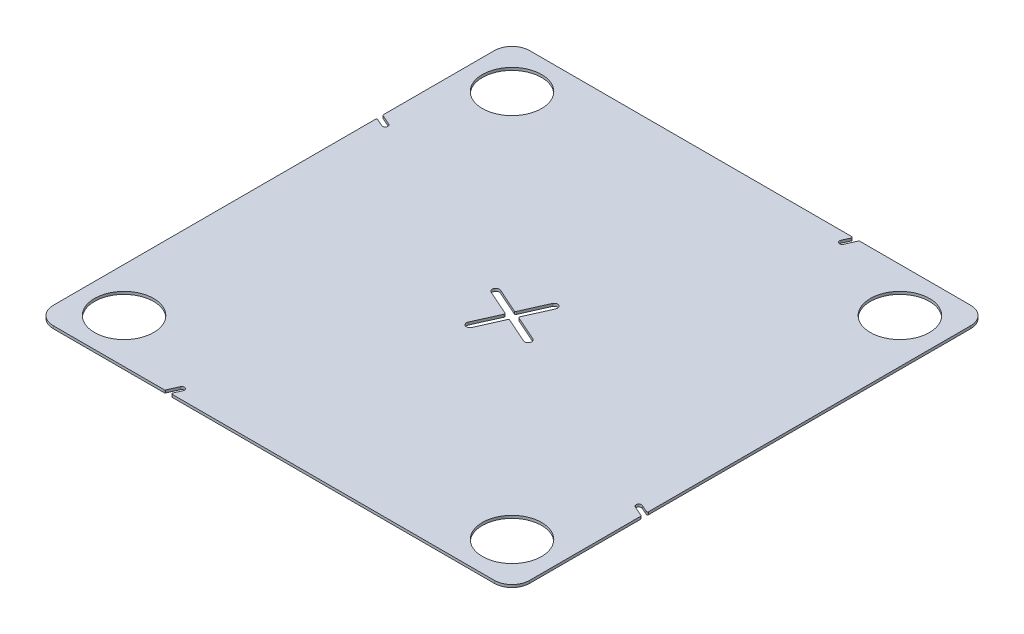
SolidWorks part; units mm, degrees
material "Plain Carbon Steel"
ref_plane "Front Plane" through (0, 0, 0) normal (0, 0, 1) x (1, 0, 0)
ref_plane "Top Plane" through (0, 0, 0) normal (0, 1, 0) x (1, 0, 0)
ref_plane "Right Plane" through (0, 0, 0) normal (1, 0, 0) x (0, 0, -1)
sketch "Sketch1" plane through (0, 0, 0) normal (0, 1, 0) x (1, 0, 0)
  line L0 (-228.092, -228.092) -> (-228.092, 228.092) construction
  line L1 (183.642, -183.642) -> (-183.642, -183.642) construction
  line L2 (183.642, -183.642) -> (183.642, 183.642) construction
  line L3 (183.642, 183.642) -> (-183.642, 183.642) construction
  line L4 (-183.642, -183.642) -> (-183.642, 183.642) construction
  line L5 (183.642, -183.642) -> (-183.642, 183.642) construction
  line L6 (183.642, 183.642) -> (-183.642, -183.642) construction
  line L7 (228.092, 228.092) -> (-228.092, 228.092) construction
  line L8 (228.092, -228.092) -> (228.092, 228.092) construction
  line L9 (228.092, -228.092) -> (-228.092, -228.092) construction
  line L11 (170.942, 170.942) -> (-170.942, 170.942)
  line L12 (170.942, 170.942) -> (170.942, -170.942)
  line L13 (170.942, -170.942) -> (-170.942, -170.942)
  line L14 (-170.942, 170.942) -> (-170.942, -170.942)
  line L15 (170.942, 170.942) -> (-170.942, -170.942) construction
  line L16 (170.942, -170.942) -> (-170.942, 170.942) construction
  point P0 (0, 0)
  point P10 (0, 0)
  dimension "D1" = 367.284
  dimension "D3" = 12.7
  dimension "D2" = 44.45
extrude "Boss-Extrude1" add sketch "Sketch1" along normal blind 1.8974
sketch "Sketch2" plane through (0, 1.8974, 0) normal (0, 1, 0) x (1, 0, 0)
  line L0 (183.642, 183.642) -> (-183.642, -183.642) construction
  line L1 (183.642, -183.642) -> (-183.642, -183.642) construction
  line L2 (183.642, -183.642) -> (-183.642, 183.642) construction
  line L3 (183.642, -183.642) -> (-183.642, 183.642) construction
  line L4 (183.642, 183.642) -> (-183.642, -183.642) construction
  circle A1 centre (-139.192, -139.192) radius 21.209
  circle A2 centre (-139.192, 139.192) radius 21.209
  circle A4 centre (139.192, 139.192) radius 21.209
  circle A6 centre (139.192, -139.192) radius 21.209
  point P26 (0, 0)
  dimension "D1" = 44.45
  dimension "D2" = 42.418
  dimension "D3" = 4
extrude "Cut-Extrude1" cut sketch "Sketch2" against normal through all
fillet "Fillet2" radius 12.7 4 edges at (170.942, 0.9487, -170.942) (-170.942, 0.9487, -170.942) (170.942, 0.9487, 170.942) (-170.942, 0.9487, 170.942)
sketch "FieldRef" plane through (0, 1.8974, 0) normal (0, 1, 0) x (1, 0, 0)
  line L0 (-76.1083, -170.942) -> (76.1083, 170.942)
  line L1 (-158.242, -170.942) -> (158.242, -170.942) construction
  line L2 (158.242, 170.942) -> (-158.242, 170.942) construction
  line L3 (170.942, -76.1083) -> (-170.942, 76.1083)
  line L4 (170.942, -158.242) -> (170.942, 158.242) construction
  line L5 (-170.942, 158.242) -> (-170.942, -158.242) construction
  dimension "D1" = 24
sketch "Sketch6" plane through (0, 1.8974, 0) normal (0, 1, 0) x (1, 0, 0)
  line L0 (6.9776, 21.9168) -> (-1.2873, 3.3535)
  line L1 (-1.2873, 3.3535) -> (-19.8505, 11.6184)
  line L2 (-76.1083, -170.942) -> (76.1083, 170.942) construction
  line L3 (170.942, -76.1083) -> (-170.942, 76.1083) construction
  line L4 (170.942, -76.1083) -> (-170.942, 76.1083) construction
  line L5 (-3.3535, -1.2873) -> (-21.9168, 6.9776)
  line L6 (-11.6184, -19.8505) -> (-3.3535, -1.2873)
  line L7 (-76.1083, -170.942) -> (76.1083, 170.942) construction
  line L8 (-6.9776, -21.9168) -> (1.2873, -3.3535)
  line L9 (1.2873, -3.3535) -> (19.8505, -11.6184)
  line L10 (3.3535, 1.2873) -> (21.9168, -6.9776)
  line L11 (11.6184, 19.8505) -> (3.3535, 1.2873)
  line L12 (-170.942, 78.1936) -> (-163.206, 74.7493)
  line L13 (-170.942, 158.242) -> (-170.942, -158.242) construction
  line L14 (-164.7556, 71.2686) -> (-170.942, 74.023)
  line L15 (-170.942, 74.023) -> (-170.942, 78.1936)
  line L16 (74.023, 170.942) -> (78.1936, 170.942)
  line L17 (78.1936, 170.942) -> (74.7493, 163.206)
  line L18 (71.2686, 164.7556) -> (74.023, 170.942)
  line L19 (170.942, -74.023) -> (170.942, -78.1936)
  line L20 (170.942, -78.1936) -> (163.206, -74.7493)
  line L21 (164.7556, -71.2686) -> (170.942, -74.023)
  line L22 (-74.023, -170.942) -> (-78.1936, -170.942)
  line L23 (-78.1936, -170.942) -> (-74.7493, -163.206)
  line L24 (-71.2686, -164.7556) -> (-74.023, -170.942)
  arc A0 (6.9776, 21.9168) -> (11.6184, 19.8505) centre (9.298, 20.8836) cw
  arc A1 (-19.8505, 11.6184) -> (-21.9168, 6.9776) centre (-20.8836, 9.298) ccw
  arc A2 (-11.6184, -19.8505) -> (-6.9776, -21.9168) centre (-9.298, -20.8836) ccw
  arc A3 (21.9168, -6.9776) -> (19.8505, -11.6184) centre (20.8836, -9.298) cw
  arc A4 (-163.206, 74.7493) -> (-164.7556, 71.2686) centre (-163.9808, 73.0089) cw
  arc A5 (74.7493, 163.206) -> (71.2686, 164.7556) centre (73.0089, 163.9808) cw
  arc A6 (163.206, -74.7493) -> (164.7556, -71.2686) centre (163.9808, -73.0089) cw
  arc A7 (-74.7493, -163.206) -> (-71.2686, -164.7556) centre (-73.0089, -163.9808) cw
  point P21 (-162.2405, 72.2341)
  point P38 (10.3311, 23.2041)
  point P46 (0, 0)
  dimension "D1" = 2.54
  dimension "D2" = 25.4
  dimension "D3" = 9.525
  dimension "D4" = 3.81
  dimension "D5" = 4
extrude "Cut-Extrude3" cut sketch "Sketch6" against normal through all
fillet "Fillet3" radius 0.762 12 edges at (1.2873, 0.9487, 3.3535) (3.3535, 0.9487, -1.2873) (-3.3535, 0.9487, 1.2873) (-1.2873, 0.9487, -3.3535) (78.1936, 0.9487, -170.942) (74.023, 0.9487, -170.942) (170.942, 0.9487, 74.023) (170.942, 0.9487, 78.1936) (-74.023, 0.9487, 170.942) (-78.1936, 0.9487, 170.942) (-170.942, 0.9487, -78.1936) (-170.942, 0.9487, -74.023)
